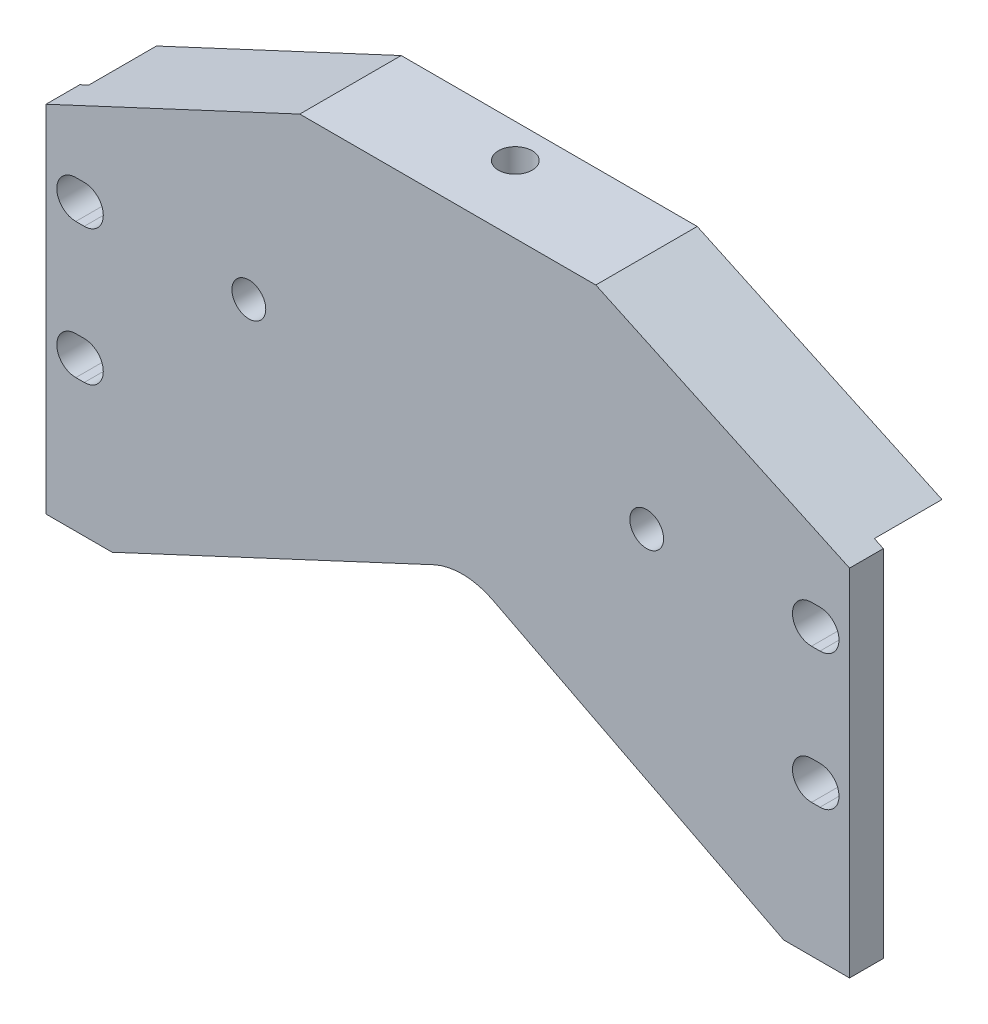
SolidWorks part; units mm, degrees
material "AISI 1018 Steel, Cold Rolled"
ref_plane "Front" through (0, 0, 0) normal (0, 0, 1) x (1, 0, 0)
ref_plane "Top" through (0, 0, 0) normal (0, 1, 0) x (1, 0, 0)
ref_plane "Right" through (0, 0, 0) normal (1, 0, 0) x (0, 0, -1)
sketch "Sketch1" plane through (0, 0, 0) normal (0, 0, 1) x (1, 0, 0)
  line L0 (58.1216, 111.0985) -> (-37.2017, 66.6485)
  line L2 (264.6574, 66.6485) -> (169.3341, 111.0985)
  line L3 (58.1216, 111.0985) -> (169.3341, 111.0985)
  line L4 (264.6574, -66.7015) -> (264.6574, 66.6485)
  line L5 (-37.2017, 66.6485) -> (-37.2017, -66.7015)
  line L6 (-37.2017, -66.7015) -> (264.6574, -66.7015)
  dimension "D1" = 115
  dimension "D2" = 177.8
  dimension "D3" = 133.35
  dimension "D4" = 115
  dimension "D5" = 133.35
  dimension "D6" = 301.8591
extrude "Base-Extrude" add sketch "Sketch1" along normal blind 12.7
hole_wizard "9/16 (0.5625) Diameter Hole1" positions "Sketch7" profile "Sketch6" hole size "9/16" standard "Ansi Inch" end condition through all
sketch "Sketch7" plane through (0, 0, 12.7) normal (0, 0, 1) x (1, 0, 0)
  line L0 (264.6574, -66.7015) -> (264.6574, 66.6485) construction
  line L3 (-37.2017, -66.7015) -> (264.6574, -66.7015) construction
  point P0 (251.9574, -9.5515)
  point P7 (251.9574, 41.2485)
  dimension "D1" = 12.7
  dimension "D2" = 57.15
  dimension "D3" = 50.8
  dimension "D4" = 12.7
sketch "Sketch6" plane through (251.9574, -9.5515, 12.7) normal (1, 0, 0) x (0, -1, 0)
  line L0 (0, 0) -> (0, 12.7)
  line L1 (0, 12.7) -> (7.1437, 12.7)
  line L2 (7.1437, 12.7) -> (7.1437, 0)
  line L5 (7.1437, 0) -> (0, 0)
  line L11 (0, -6.35) -> (0, 107.95) construction
  dimension "Thru Hole Dia." = 14.2875
  dimension "Thru Hole Depth" = 12.7
sketch "Sketch8" plane through (0, 0, 12.7) normal (0, 0, 1) x (1, 0, 0)
  line L1 (-37.2017, -66.7015) -> (264.6574, -66.7015) construction
  line L2 (-12.3714, -66.7015) -> (239.908, -66.7015)
  line L9 (108.401, -10.3844) -> (-12.3714, -66.7015)
  line L16 (130.7108, -10.7955) -> (239.908, -66.7015)
  arc A0 (130.7108, -10.7955) -> (108.401, -10.3844) centre (119.1355, -33.4046) ccw
  dimension "D1" = 25.4
extrude "Cut-Extrude1" cut sketch "Sketch8" against normal through all
ref_plane "Plane4" through (-37.2017, 0, 0) normal (1, 0, 0) x (0, 0, -1)
ref_plane "Plane5" through (113.7683, 0, 0) normal (1, 0, 0) x (0, 0, -1)
mirror "Mirror3" about plane through (113.7683, 0, 0) normal (1, 0, 0) of "9/16 (0.5625) Diameter Hole1"
sketch "Sketch10" plane through (0, 0, 0) normal (0, 0, -1) x (-1, 0, 0)
  line L0 (-169.3341, 111.0985) -> (-58.1216, 111.0985) construction
  line L1 (-169.3341, 111.0985) -> (-58.1216, 111.0985)
  line L2 (-58.1216, 111.0985) -> (37.2017, 66.6485) construction
  line L3 (-58.1216, 111.0985) -> (33.8245, 68.2233)
  line L4 (-264.6574, 66.6485) -> (-169.3341, 111.0985) construction
  line L5 (-261.2802, 68.2233) -> (-169.3341, 111.0985)
  line L6 (-261.2802, 68.2233) -> (33.8245, 68.2233)
  dimension "D1" = 42.8752
extrude "Boss-Extrude1" add sketch "Sketch10" along normal blind 25.4
hole_wizard "1/2-20 Tapped Hole1" positions "Sketch12" profile "Sketch11" tap size "1/2-20" standard "Ansi Inch" end condition through all
sketch "Sketch12" plane through (0, 111.0985, 0) normal (0, 1, 0) x (-1, 0, 0)
  line L0 (-58.1216, 12.7) -> (-58.1216, -25.4) construction
  line L1 (-58.1216, -25.4) -> (-169.3341, -25.4) construction
  point P0 (-113.6968, -12.7)
  dimension "D1" = 55.5752
  dimension "D2" = 12.7
sketch "Sketch11" plane through (113.6968, 111.0985, -12.7) normal (1, 0, 0) x (0, 0, 1)
  line L0 (0, 0) -> (0, 177.8)
  line L1 (0, 177.8) -> (6.35, 177.8)
  line L2 (6.35, 177.8) -> (6.35, 0)
  line L5 (6.35, 0) -> (0, 0)
  line L11 (0, -6.35) -> (0, 107.95) construction
  dimension "Thread Major Dia." = 12.7
  dimension "Thru Tap Drill Depth" = 177.8
sketch "Sketch13" plane through (0, 0, 12.7) normal (0, 0, 1) x (1, 0, 0)
  line L0 (250.3699, -2.4078) -> (253.5449, -2.4078)
  line L1 (253.5449, -16.6953) -> (250.3699, -16.6953)
  arc A1 (250.3699, -2.4078) -> (250.3699, -16.6953) centre (250.3699, -9.5515) ccw
  arc A2 (253.5449, -16.6953) -> (253.5449, -2.4078) centre (253.5449, -9.5515) ccw
extrude "Cut-Extrude2" cut sketch "Sketch13" against normal through all
sketch "Sketch14" plane through (0, 0, 12.7) normal (0, 0, 1) x (1, 0, 0)
  line L0 (253.5449, 48.3922) -> (250.3699, 48.3922)
  line L1 (250.3699, 34.1047) -> (253.5449, 34.1047)
  line L2 (250.3699, 41.2485) -> (253.5449, 41.2485) construction
  line L3 (253.5449, 41.2485) -> (253.5449, -9.5515) construction
  line L4 (250.3699, 41.2485) -> (250.3699, -9.5515) construction
  line L5 (250.3699, -9.5515) -> (253.5449, -9.5515) construction
  arc A2 (253.5449, 34.1047) -> (253.5449, 48.3922) centre (253.5449, 41.2485) ccw
  arc A3 (250.3699, 48.3922) -> (250.3699, 34.1047) centre (250.3699, 41.2485) ccw
  dimension "D1" = 50.8
extrude "Cut-Extrude3" cut sketch "Sketch14" against normal through all
mirror "Mirror4" about plane through (113.7683, 0, 0) normal (1, 0, 0) of "Cut-Extrude3", "Cut-Extrude2"
hole_wizard "1/2-20 Tapped Hole2" positions "Sketch16" profile "Sketch15" tap size "1/2-20" standard "Ansi Inch" end condition through all
sketch "Sketch16" plane through (0, 0, 12.7) normal (0, 0, 1) x (1, 0, 0)
  line L0 (-37.2017, -20.955) -> (-37.2017, 20.955) construction
  line L1 (-37.2017, -66.7015) -> (-12.3714, -66.7015) construction
  line L2 (264.6574, -66.7015) -> (264.6574, 66.6485) construction
  line L3 (239.908, -66.7015) -> (264.6574, -66.7015) construction
  point P0 (38.9983, 41.2485)
  point P5 (188.4574, 41.2485)
  dimension "D1" = 76.2
  dimension "D2" = 107.95
  dimension "D3" = 76.2
  dimension "D4" = 107.95
sketch "Sketch15" plane through (38.9983, 41.2485, 12.7) normal (1, 0, 0) x (0, -1, 0)
  line L0 (0, 0) -> (0, 38.1)
  line L1 (0, 38.1) -> (6.35, 38.1)
  line L2 (6.35, 38.1) -> (6.35, 0)
  line L5 (6.35, 0) -> (0, 0)
  line L11 (0, -6.35) -> (0, 107.95) construction
  dimension "Thread Major Dia." = 12.7
  dimension "Thru Tap Drill Depth" = 38.1
sketch "Sketch17" plane through (0, 0, -25.4) normal (0, 0, -1) x (-1, 0, 0)
  line L0 (-261.2802, 68.2233) -> (33.8245, 68.2233) construction
  line L1 (-129.6029, 68.2233) -> (-97.8529, 68.2233)
  line L5 (-129.6029, 88.8481) -> (-129.6029, 68.2233)
  line L6 (-97.8529, 88.8481) -> (-97.8529, 68.2233)
  line L7 (-124.8277, 93.6233) -> (-102.6281, 93.6233)
  arc A0 (-124.8277, 93.6233) -> (-129.6029, 88.8481) centre (-124.8277, 88.8481) ccw
  arc A1 (-97.8529, 88.8481) -> (-102.6281, 93.6233) centre (-102.6281, 88.8481) ccw
  dimension "D1" = 4.7752
  dimension "D3" = 25.4
extrude "Cut-Extrude4" cut sketch "Sketch17" against normal blind 25.4
